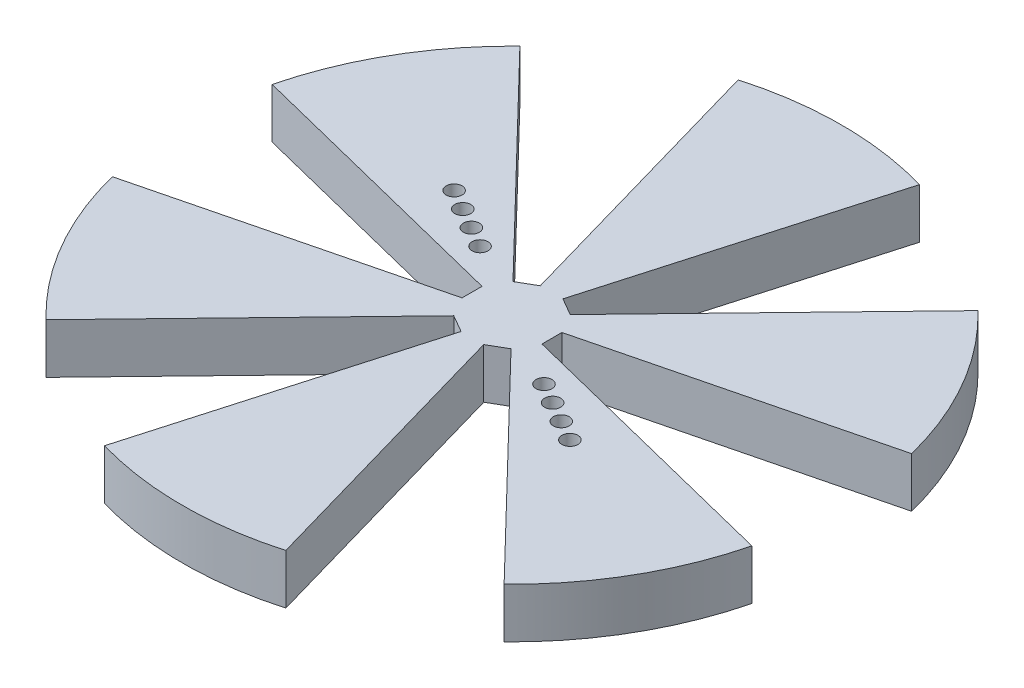
SolidWorks part; units mm, degrees
ref_plane "Front Plane" through (0, 0, 0) normal (0, 0, 1) x (1, 0, 0)
ref_plane "Top Plane" through (0, 0, 0) normal (0, 1, 0) x (1, 0, 0)
ref_plane "Right Plane" through (0, 0, 0) normal (1, 0, 0) x (0, 0, -1)
sketch "Sketch1" plane through (0, 0, 0) normal (0, 1, 0) x (1, 0, 0)
  circle A0 centre (0, 0) radius 41.91
  dimension "D1" = 83.82
extrude "Boss-Extrude1" add sketch "Sketch1" along normal blind 6.35
sketch "Sketch2" plane through (0, 6.35, 0) normal (0, 1, 0) x (1, 0, 0)
  line L0 (40.6598, -10.16) -> (5.08, -1.2694)
  line L1 (0, 0) -> (5.08, 1.2694) construction
  line L2 (40.6598, -10.16) -> (40.6598, 10.16) construction
  line L3 (13.8396, 0) -> (41.91, 0) construction
  line L4 (5.08, 1.2694) -> (5.08, -1.2694)
  line L5 (-1.4407, -5.0341) -> (-11.5311, -40.2925)
  line L6 (5.08, 1.2694) -> (40.6598, 10.16)
  line L7 (5.08, -1.2694) -> (0, 0) construction
  line L8 (-29.1287, -30.1325) -> (-3.6393, -3.7647)
  line L9 (5.08, 0) -> (13.8396, 0) construction
  line L10 (3.6393, -3.7647) -> (29.1287, -30.1325)
  line L11 (1.4407, -5.0341) -> (3.6393, -3.7647)
  line L12 (11.5311, -40.2925) -> (1.4407, -5.0341)
  line L13 (-5.08, -1.2694) -> (-40.6598, -10.16)
  line L14 (-40.6598, 10.16) -> (-5.08, 1.2694)
  line L15 (-3.6393, 3.7647) -> (-29.1287, 30.1325)
  line L16 (-11.5311, 40.2925) -> (-1.4407, 5.0341)
  line L17 (1.4407, 5.0341) -> (11.5311, 40.2925)
  line L18 (29.1287, 30.1325) -> (3.6393, 3.7647)
  line L19 (3.6393, -3.7647) -> (1.4407, -5.0341)
  line L20 (-1.4407, -5.0341) -> (-3.6393, -3.7647)
  line L21 (-5.08, -1.2694) -> (-5.08, 1.2694)
  line L22 (-3.6393, 3.7647) -> (-1.4407, 5.0341)
  line L23 (1.4407, 5.0341) -> (3.6393, 3.7647)
  arc A0 (40.6598, 10.16) -> (40.6598, -10.16) centre (0, 0) cw
  circle A1 centre (0, 0) radius 41.91 construction
  arc A2 (29.1287, -30.1325) -> (11.5311, -40.2925) centre (0, 0) cw
  arc A3 (-11.5311, -40.2925) -> (-29.1287, -30.1325) centre (0, 0) cw
  arc A4 (-40.6598, -10.16) -> (-40.6598, 10.16) centre (0, 0) cw
  arc A5 (-29.1287, 30.1325) -> (-11.5311, 40.2925) centre (0, 0) cw
  arc A6 (11.5311, 40.2925) -> (29.1287, 30.1325) centre (0, 0) cw
  circle A12 centre (0, 0) radius 5.08 construction
  circle A14 centre (0, 0) radius 3.1024 construction
  point P56 (0, 0)
  circle M14 centre (0, 0) radius 41.91
  dimension "D2" = 10.16
  dimension "D1" = 20.32
  dimension "D5" = 6
extrude "Cut-Extrude1" cut sketch "Sketch2" against normal through all contours L15 L22 L16 M14 | L17 L23 L18 M14 | L6 L4 L0 M14 | L12 L10 L11 M14 | L5 L20 L8 M14 | L13 L21 L14 M14
sketch "Sketch3" plane through (0, 6.35, 0) normal (0, 1, 0) x (1, 0, 0)
  line L0 (0, 11.1125) -> (0, -11.1125) construction
  line L1 (-11.1125, 0) -> (11.1125, 0) construction
  line L2 (-9.6237, 5.5562) -> (9.6237, -5.5562) construction
  line L3 (-3.6393, 3.7647) -> (-5.08, 1.2694) construction
  line L4 (5.5562, 9.6237) -> (-5.5562, -9.6237) construction
  line L5 (-9.6237, 5.5562) -> (-12.2218, 7.0562) construction
  line L6 (-12.2218, 7.0562) -> (-14.8199, 8.5562) construction
  line L7 (-14.8199, 8.5562) -> (-17.4179, 10.0562) construction
  circle A0 centre (11.1125, 0) radius 1.016 construction
  circle A1 centre (-11.1125, 0) radius 1.016 construction
  circle A2 centre (0, 11.1125) radius 1.016 construction
  circle A3 centre (0, -11.1125) radius 1.016 construction
  circle A4 centre (0, 0) radius 5.2362 construction
  circle A5 centre (-9.6237, 5.5562) radius 1.016
  circle A6 centre (9.6237, -5.5562) radius 1.016
  circle A7 centre (-5.5562, -9.6237) radius 1.016
  circle A8 centre (5.5562, 9.6237) radius 1.016
  circle A9 centre (-9.6237, 5.5562) radius 1.016
  circle A10 centre (9.6237, -5.5562) radius 1.016
  circle A11 centre (5.5562, 9.6237) radius 1.016
  circle A12 centre (-5.5562, -9.6237) radius 1.016
  circle A13 centre (-12.2218, 7.0562) radius 1.016
  circle A14 centre (-14.8199, 8.5562) radius 1.016
  circle A15 centre (-17.4179, 10.0562) radius 1.016
  circle A16 centre (7.0562, 12.2218) radius 1.016
  circle A17 centre (8.5562, 14.8199) radius 1.016
  circle A18 centre (10.0562, 17.4179) radius 1.016
  circle A19 centre (12.2218, -7.0562) radius 1.016
  circle A20 centre (14.8199, -8.5562) radius 1.016
  circle A21 centre (17.4179, -10.0562) radius 1.016
  circle A22 centre (-7.0562, -12.2218) radius 1.016
  circle A23 centre (-8.5562, -14.8199) radius 1.016
  circle A24 centre (-10.0562, -17.4179) radius 1.016
  point P10 (0, 0)
  point P16 (-4.3597, 2.517)
  point P37 (0, 0)
  point P41 (14.2217, 14.2217)
  point P42 (0, 0)
  point P43 (0, 0)
  point P63 (0, 0)
  point P64 (0, 0)
  point P65 (0, 0)
  point P67 (0, 0)
  dimension "D2" = 2.032
  dimension "D1" = 22.225
  dimension "D5" = 3
  dimension "D3" = 2
  dimension "D4" = 4
extrude "Cut-Extrude2" cut sketch "Sketch3" against normal through all contours A21 | A22 | A23 | A24 | A5 | A8 | A6 | A7 | A14 | A15 | A13 | A16 | A17 | A18 | A19 | A20
sketch "Sketch8" [suppressed] plane through (0, 6.35, 0) normal (0, 1, 0) x (1, 0, 0)
  line L0 (-7.8577, 7.8577) -> (7.8577, -7.8577) construction
  circle A0 centre (0, 0) radius 43.18 construction
  point P7 (0, 0)
  line B0 (-30.6646, 30.6646) -> (-33.4676, 33.4676) construction
  line B1 (-35.3726, 31.5626) -> (-35.3726, 24.7647)
  line B2 (-31.5626, 35.3726) -> (-24.7647, 35.3726)
  arc B3 (-31.5626, 35.3726) -> (-35.3726, 31.5626) centre (-31.5626, 31.5626) ccw
  arc B4 (-24.7647, 35.3726) -> (-35.3726, 24.7647) centre (-6.7644, 6.7644) ccw
  line B5 (31.5626, 35.3726) -> (24.7647, 35.3726)
  line B6 (35.3726, 31.5626) -> (35.3726, 24.7647)
  arc B7 (35.3726, 31.5626) -> (31.5626, 35.3726) centre (31.5626, 31.5626) ccw
  arc B8 (35.3726, 24.7647) -> (24.7647, 35.3726) centre (6.7644, 6.7644) ccw
  line B9 (35.3726, -31.5626) -> (35.3726, -24.7647)
  line B10 (31.5626, -35.3726) -> (24.7647, -35.3726)
  arc B11 (31.5626, -35.3726) -> (35.3726, -31.5626) centre (31.5626, -31.5626) ccw
  arc B12 (24.7647, -35.3726) -> (35.3726, -24.7647) centre (6.7644, -6.7644) ccw
  line B13 (-31.5626, -35.3726) -> (-24.7647, -35.3726)
  line B14 (-35.3726, -31.5626) -> (-35.3726, -24.7647)
  arc B15 (-35.3726, -31.5626) -> (-31.5626, -35.3726) centre (-31.5626, -31.5626) ccw
  arc B16 (-35.3726, -24.7647) -> (-24.7647, -35.3726) centre (-6.7644, -6.7644) ccw
  dimension "D1" = 4
sketch_block_instance "Block-tabHub-1"
sketch_block "Block-tabHub" parameters "D1"=3.81, "D2"=5.08, "D3"=90
sketch_block_instance "Block-tabHub-3"
sketch_block_instance "Block-tabHub-4"
sketch_block_instance "Block-tabHub-5"
extrude "Boss-Extrude2" [suppressed] add sketch "Sketch8" against normal up to surface (6.35 mm away)
